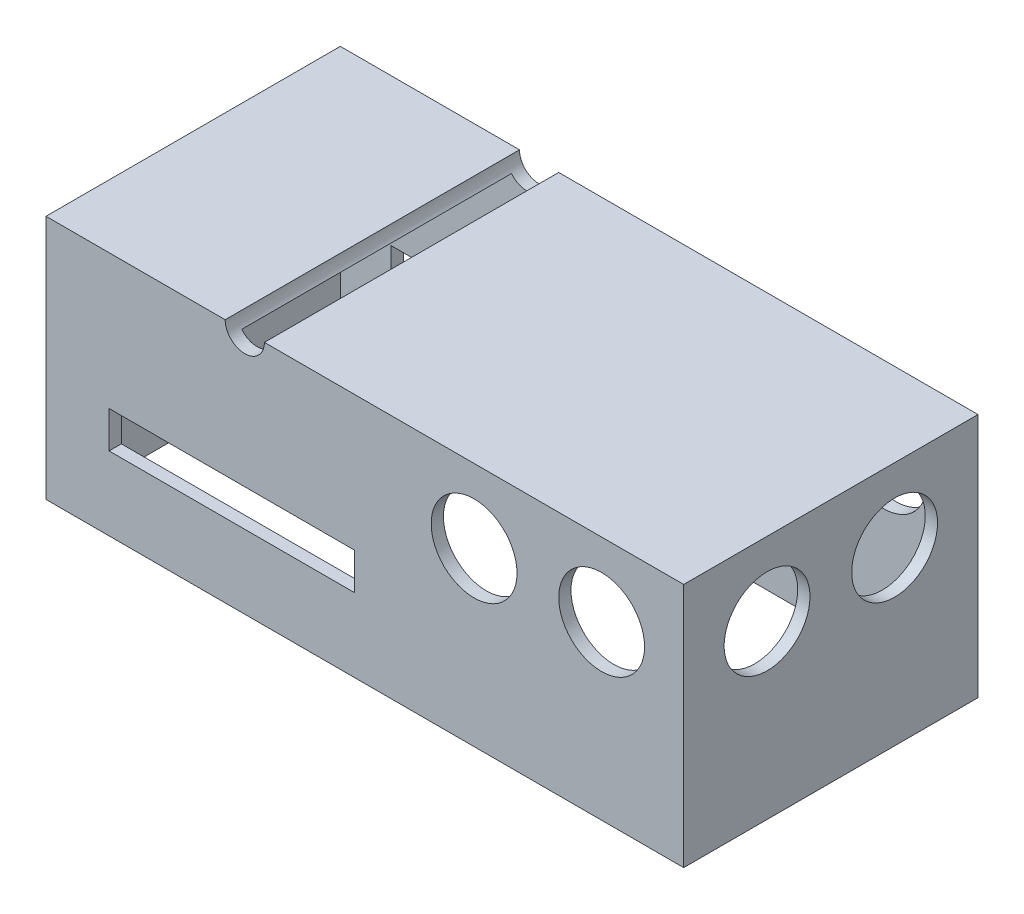
SolidWorks part; units mm, degrees
ref_plane "Front Plane" through (0, 0, 0) normal (0, 0, 1) x (1, 0, 0)
ref_plane "Top Plane" through (0, 0, 0) normal (0, 1, 0) x (1, 0, 0)
ref_plane "Right Plane" through (0, 0, 0) normal (1, 0, 0) x (0, 0, -1)
sketch "Sketch1" plane through (0, 0, 0) normal (0, 1, 0) x (1, 0, 0)
  line L1 (65, -30) -> (-65, -30)
  line L2 (65, -30) -> (65, 30)
  line L3 (65, 30) -> (-65, 30)
  line L4 (-65, -30) -> (-65, 30)
  line L5 (65, -30) -> (-65, 30) construction
  line L6 (65, 30) -> (-65, -30) construction
  line L11 (62.8333, -29) -> (-62.8333, 29) construction
  line L12 (62.8333, 29) -> (-62.8333, -29) construction
  point P1 (0, 0)
  point P6 (0, 0)
  dimension "D1" = 60
  dimension "D2" = 130
extrude "Boss-Extrude2" add sketch "Sketch1" along normal blind 50
shell "Shell1" thickness 2.5
sketch "Sketch2" plane through (65, 0, 0) normal (1, 0, 0) x (0, 0, -1)
  line L0 (0, 0) -> (0, 35)
  line L1 (0, 35) -> (4.25, 35)
  line L2 (0, 35) -> (-4.25, 35)
  circle A0 centre (13, 35) radius 8.75
  circle A1 centre (-13, 35) radius 8.75
  dimension "D4" = 17.5
  dimension "D5" = 17.5
  dimension "D1" = 35
extrude "Cut-Extrude1" cut sketch "Sketch2" against normal up to next contours L2 A1 | L2 A1 | L1 A0 | L1 A0
sketch "Sketch3" plane through (0, 0, 30) normal (0, 0, 1) x (1, 0, 0)
  line L0 (35.2742, 0) -> (35.2742, 35)
  line L1 (35.2742, 35) -> (39.5242, 35)
  line L2 (35.2742, 35) -> (31.0242, 35)
  circle A0 centre (48.2742, 35) radius 8.75
  circle A1 centre (22.2742, 35) radius 8.75
  dimension "D1" = 17.5
  dimension "D2" = 17.5
extrude "Cut-Extrude2" cut sketch "Sketch3" against normal through all contours A1 | A0
sketch "Sketch4" plane through (0, 0, -30) normal (0, 0, -1) x (-1, 0, 0)
  line L1 (2.1407, 22.5) -> (52.1407, 22.5)
  line L2 (2.1407, 22.5) -> (2.1407, 15)
  line L3 (2.1407, 15) -> (52.1407, 15)
  line L4 (52.1407, 22.5) -> (52.1407, 15)
  dimension "D1" = 7.5
  dimension "D2" = 50
extrude "Cut-Extrude3" cut sketch "Sketch4" against normal through all
sketch "Sketch5" plane through (0, 0, -30) normal (0, 0, -1) x (-1, 0, 0)
  line L0 (20.4758, 50) -> (28.4758, 50)
  line L3 (-65, 50) -> (65, 50) construction
  line L4 (-13.5242, 35) -> (-13.5242, 50)
  arc A0 (20.4758, 50) -> (28.4758, 50) centre (24.4758, 50) ccw
  circle A1 centre (-22.2742, 35) radius 8.75 construction
  dimension "D1" = 4
  dimension "D2" = 34
extrude "Cut-Extrude4" cut sketch "Sketch5" against normal through all contours L0 A0
